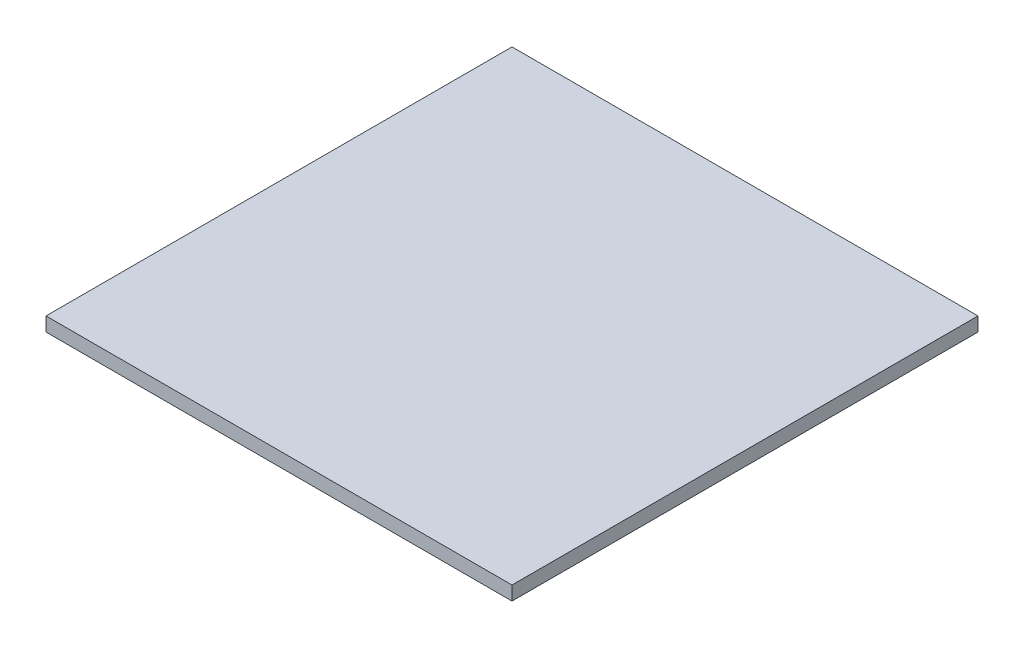
SolidWorks part; units mm, degrees
ref_plane "前视基准面" through (0, 0, 0) normal (0, 0, 1) x (1, 0, 0)
ref_plane "上视基准面" through (0, 0, 0) normal (0, 1, 0) x (1, 0, 0)
ref_plane "右视基准面" through (0, 0, 0) normal (1, 0, 0) x (0, 0, -1)
sketch "草图1" plane through (0, 0, 0) normal (0, 1, 0) x (1, 0, 0)
  line L1 (-50, 50) -> (50, 50)
  line L2 (-50, 50) -> (-50, -50)
  line L3 (-50, -50) -> (50, -50)
  line L4 (50, 50) -> (50, -50)
  line L5 (-50, 50) -> (50, -50) construction
  line L6 (-50, -50) -> (50, 50) construction
  point P0 (0, 0)
  dimension "D1" = 100
  dimension "D2" = 100
extrude "凸台-拉伸1" add sketch "草图1" along normal blind 3
